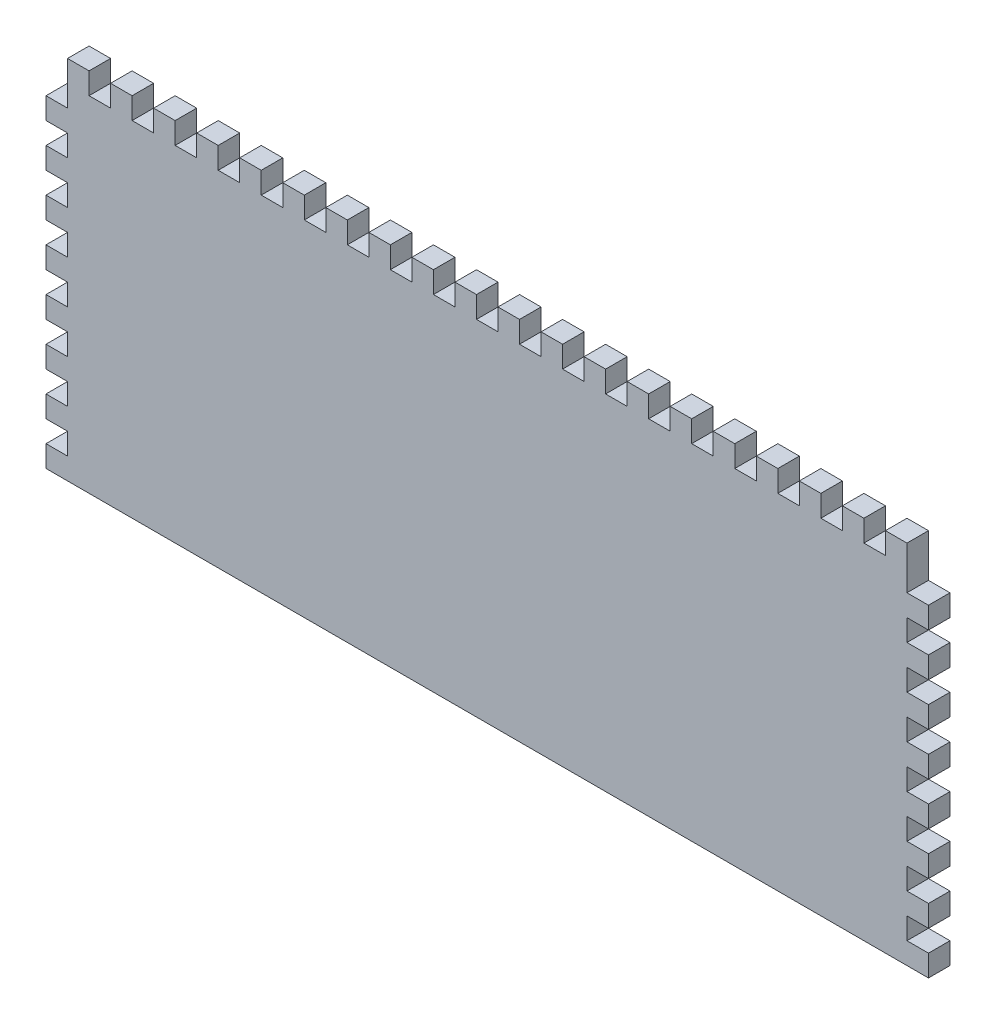
SolidWorks part; units mm, degrees
ref_plane "Front Plane" through (0, 0, 0) normal (0, 0, 1) x (1, 0, 0)
ref_plane "Top Plane" through (0, 0, 0) normal (0, 1, 0) x (1, 0, 0)
ref_plane "Right Plane" through (0, 0, 0) normal (1, 0, 0) x (0, 0, -1)
sketch "Sketch1" plane through (0, 0, 0) normal (0, 0, 1) x (1, 0, 0)
  line L1 (-130.175, -53.975) -> (130.175, -53.975)
  line L2 (-130.175, -53.975) -> (-130.175, 53.975)
  line L3 (-130.175, 53.975) -> (130.175, 53.975)
  line L4 (130.175, -53.975) -> (130.175, 53.975)
  line L5 (-130.175, -53.975) -> (130.175, 53.975) construction
  line L6 (-130.175, 53.975) -> (130.175, -53.975) construction
  point P0 (0, 0)
  dimension "D1" = 107.95
  dimension "D2" = 260.35
extrude "Boss-Extrude1" add sketch "Sketch1" along normal blind 6.35
sketch "Sketch3" plane through (0, 0, 6.35) normal (0, 0, 1) x (1, 0, 0)
  line L0 (130.175, -53.975) -> (130.175, 53.975) construction
  line L1 (130.175, -41.275) -> (123.825, -41.275)
  line L2 (130.175, -41.275) -> (130.175, -47.625)
  line L3 (130.175, -47.625) -> (123.825, -47.625)
  line L4 (123.825, -41.275) -> (123.825, -47.625)
  dimension "D1" = 6.35
  dimension "D2" = 6.35
  dimension "D3" = 6.35
extrude "Cut-Extrude1" cut sketch "Sketch3" against normal through all
pattern_linear "LPattern1" count 8 spacing 12.7 along (0, 1, 0) of "Cut-Extrude1"
mirror "Mirror1" about plane through (0, 0, 0) normal (1, 0, 0) of "LPattern1", "Cut-Extrude1"
sketch "Sketch4" plane through (0, 0, 6.35) normal (0, 0, 1) x (1, 0, 0)
  line L1 (-130.175, 53.975) -> (-123.825, 53.975)
  line L2 (-130.175, 53.975) -> (-130.175, 47.625)
  line L3 (-130.175, 47.625) -> (-123.825, 47.625)
  line L4 (-123.825, 53.975) -> (-123.825, 47.625)
extrude "Cut-Extrude2" cut sketch "Sketch4" against normal blind 6.35
pattern_linear "LPattern2" count 21 spacing 12.7 along (1, 0, 0) of "Cut-Extrude2"
